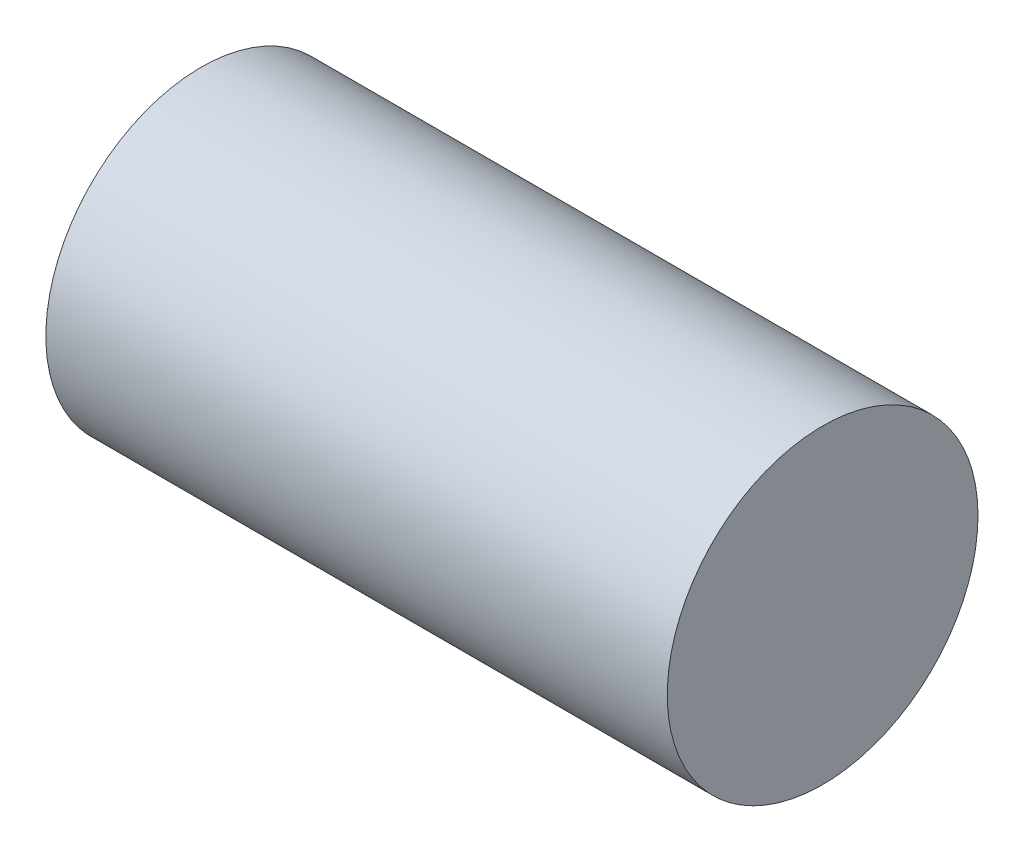
SolidWorks part; units mm, degrees
ref_plane "Front Plane" through (0, 0, 0) normal (0, 0, 1) x (1, 0, 0)
ref_plane "Top Plane" through (0, 0, 0) normal (0, 1, 0) x (1, 0, 0)
ref_plane "Right Plane" through (0, 0, 0) normal (1, 0, 0) x (0, 0, -1)
sketch "Sketch1" plane through (0, 0, 0) normal (1, 0, 0) x (0, 0, -1)
  circle A0 centre (0, 0) radius 2.3813
  dimension "D1" = 4.7625
extrude "Boss-Extrude1" add sketch "Sketch1" along normal blind 9.525 contours A0
